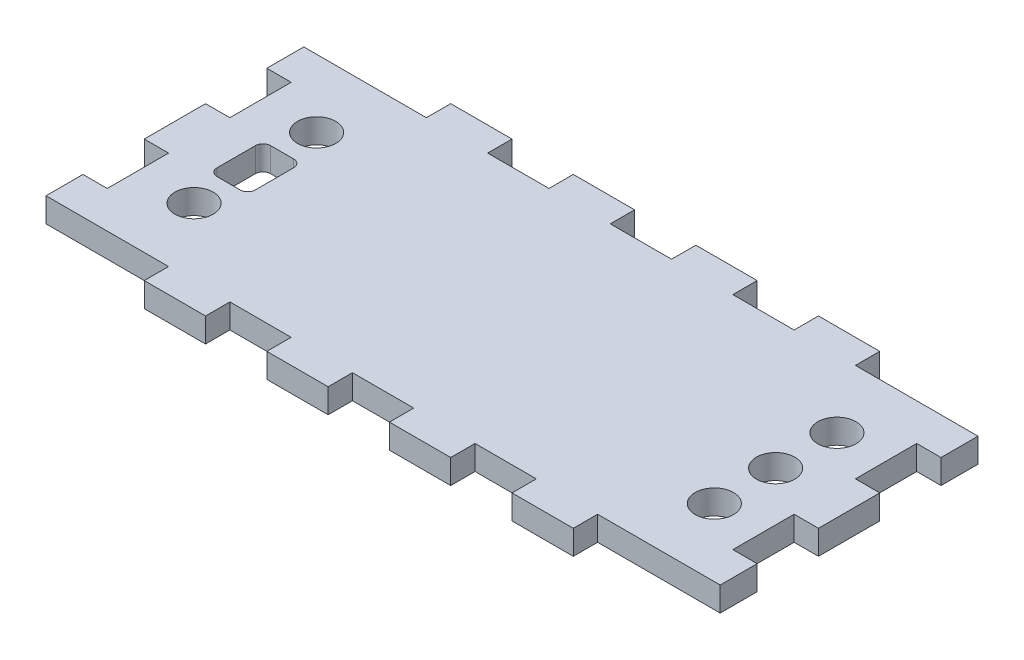
SolidWorks part; units mm, degrees
ref_plane "Front Plane" through (0, 0, 0) normal (0, 0, 1) x (1, 0, 0)
ref_plane "Top Plane" through (0, 0, 0) normal (0, 1, 0) x (1, 0, 0)
ref_plane "Right Plane" through (0, 0, 0) normal (1, 0, 0) x (0, 0, -1)
sketch "Sketch1" plane through (0, 0, 0) normal (0, 1, 0) x (1, 0, 0)
  line L1 (0, 0) -> (88, 0)
  line L2 (0, 0) -> (0, -40)
  line L3 (0, -40) -> (88, -40)
  line L4 (88, 0) -> (88, -40)
  dimension "D1" = 40
  dimension "D2" = 88
extrude "Boss-Extrude1" add sketch "Sketch1" along normal blind 3.175
sketch "Sketch2" plane through (0, 3.175, 0) normal (0, 1, 0) x (1, 0, 0)
  line L0 (44, 0) -> (44, -40) construction
  line L1 (88, 0) -> (0, 0) construction
  line L2 (0, -40) -> (88, -40) construction
  line L3 (0, -20) -> (88, -20) construction
  line L4 (0, 0) -> (0, -40) construction
  line L5 (88, -40) -> (88, 0) construction
  line L6 (16, 0) -> (16, -3.175)
  line L7 (40, 0) -> (48, 0)
  line L8 (0, -3.175) -> (16, -3.175)
  line L9 (40, -3.175) -> (48, -3.175)
  line L10 (48, 0) -> (48, -3.175)
  line L11 (56, 0) -> (64, 0)
  line L12 (56, 0) -> (56, -3.175)
  line L13 (56, -3.175) -> (64, -3.175)
  line L14 (64, 0) -> (64, -3.175)
  line L15 (88, 0) -> (72, 0)
  line L16 (88, 0) -> (88, -3.175)
  line L17 (88, -3.175) -> (72, -3.175)
  line L18 (72, 0) -> (72, -3.175)
  line L19 (0, 0) -> (0, -3.175)
  line L20 (0, 0) -> (16, 0)
  line L21 (24, 0) -> (24, -3.175)
  line L22 (32, -3.175) -> (24, -3.175)
  line L23 (32, 0) -> (32, -3.175)
  line L24 (32, 0) -> (24, 0)
  line L25 (40, 0) -> (40, -3.175)
  line L26 (40, -40) -> (40, -36.825)
  line L27 (32, -40) -> (24, -40)
  line L28 (32, -40) -> (32, -36.825)
  line L29 (32, -36.825) -> (24, -36.825)
  line L30 (24, -40) -> (24, -36.825)
  line L31 (0, -40) -> (16, -40)
  line L32 (0, -40) -> (0, -36.825)
  line L33 (72, -40) -> (72, -36.825)
  line L34 (88, -36.825) -> (72, -36.825)
  line L35 (88, -40) -> (88, -36.825)
  line L36 (88, -40) -> (72, -40)
  line L37 (64, -40) -> (64, -36.825)
  line L38 (56, -36.825) -> (64, -36.825)
  line L39 (56, -40) -> (56, -36.825)
  line L40 (56, -40) -> (64, -40)
  line L41 (48, -40) -> (48, -36.825)
  line L42 (40, -36.825) -> (48, -36.825)
  line L43 (0, -36.825) -> (16, -36.825)
  line L44 (40, -40) -> (48, -40)
  line L45 (16, -40) -> (16, -36.825)
  point P34 (44, -3.175)
  point P54 (44, -36.825)
  dimension "D1" = 4
  dimension "D2" = 3.175
  dimension "D3" = 3.175
  dimension "D4" = 8
  dimension "D5" = 8
  dimension "D6" = 3.175
  dimension "D7" = 8
extrude "Cut-Extrude1" cut sketch "Sketch2" against normal up to next
sketch "Sketch3" plane through (0, 3.175, 0) normal (0, 1, 0) x (1, 0, 0)
  line L0 (0, -20) -> (88, -20) construction
  line L1 (0, -3.175) -> (0, -36.825) construction
  line L2 (88, -36.825) -> (88, -3.175) construction
  line L3 (3.175, -24) -> (3.175, -32)
  line L4 (0, -16) -> (3.175, -16)
  line L5 (0, -16) -> (0, -8)
  line L6 (0, -8) -> (3.175, -8)
  line L7 (3.175, -16) -> (3.175, -8)
  line L8 (0, -32) -> (3.175, -32)
  line L9 (0, -24) -> (0, -32)
  line L10 (0, -24) -> (3.175, -24)
  line L11 (44, -3.175) -> (44, -36.825) construction
  line L12 (40, -3.175) -> (48, -3.175) construction
  line L13 (48, -36.825) -> (40, -36.825) construction
  line L14 (88, -24) -> (84.825, -24)
  line L15 (88, -24) -> (88, -32)
  line L16 (88, -32) -> (84.825, -32)
  line L17 (84.825, -16) -> (84.825, -8)
  line L18 (88, -8) -> (84.825, -8)
  line L19 (88, -16) -> (88, -8)
  line L20 (88, -16) -> (84.825, -16)
  line L21 (84.825, -24) -> (84.825, -32)
  dimension "D1" = 8
  dimension "D2" = 3.175
  dimension "D3" = 4
extrude "Cut-Extrude2" cut sketch "Sketch3" against normal up to next
sketch "Sketch4" plane through (0, 3.175, 0) normal (0, 1, 0) x (1, 0, 0)
  line L4 (44, -3.175) -> (44, -36.825) construction
  line L5 (40, -3.175) -> (48, -3.175) construction
  line L6 (48, -36.825) -> (40, -36.825) construction
  line L7 (78.41, -3.175) -> (78.41, -36.825) construction
  circle A3 centre (78.41, -28) radius 2.5
  circle A4 centre (78.41, -12) radius 2.5
  circle A5 centre (78.41, -20) radius 2.5
extrude "Cut-Extrude3" cut sketch "Sketch4" against normal up to next
sketch "Sketch5" plane through (0, 3.175, 0) normal (0, 1, 0) x (1, 0, 0)
  line L0 (8, -3.175) -> (8, -36.825) construction
  line L1 (0, -3.175) -> (16, -3.175) construction
  line L2 (16, -36.825) -> (0, -36.825) construction
  line L4 (9, -16.5) -> (12, -16.5)
  line L5 (8, -17.5) -> (8, -22.5)
  line L6 (9, -23.5) -> (12, -23.5)
  line L7 (13, -17.5) -> (13, -22.5)
  arc A0 (8, -22.5) -> (9, -23.5) centre (9, -22.5) ccw
  arc A1 (12, -23.5) -> (13, -22.5) centre (12, -22.5) ccw
  arc A2 (12, -16.5) -> (13, -17.5) centre (12, -17.5) cw
  arc A3 (8, -17.5) -> (9, -16.5) centre (9, -17.5) cw
  circle A4 centre (10.5, -12) radius 2.5
  circle A5 centre (10.5, -28) radius 2.5
  point P10 (8, -20)
  point P11 (8, -20)
  point P14 (8, -23.5)
  point P17 (13, -23.5)
  point P20 (13, -16.5)
  point P23 (8, -16.5)
  dimension "D4" = 1
  dimension "D5" = 5
  dimension "D1" = 5
  dimension "D2" = 7
  dimension "D3" = 0
  dimension "D6" = 8
  dimension "D7" = 2
extrude "Cut-Extrude4" cut sketch "Sketch5" against normal up to next
